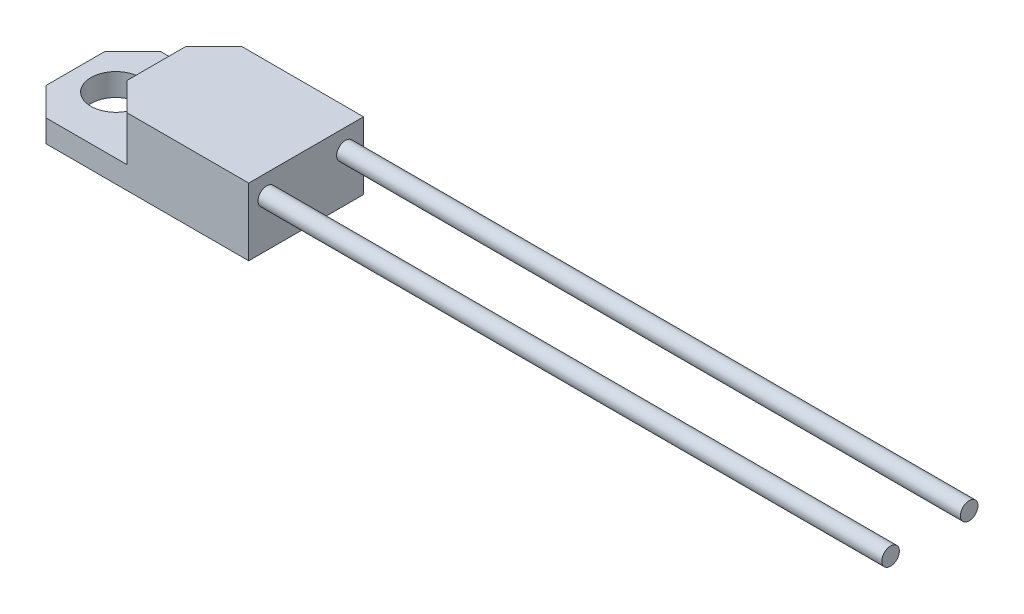
SolidWorks part; units mm, degrees
ref_plane "Front Plane" through (0, 0, 0) normal (0, 0, 1) x (1, 0, 0)
ref_plane "Top Plane" through (0, 0, 0) normal (0, 1, 0) x (1, 0, 0)
ref_plane "Right Plane" through (0, 0, 0) normal (1, 0, 0) x (0, 0, -1)
sketch "Sketch1" plane through (0, 0, 0) normal (0, 1, 0) x (1, 0, 0)
  line L1 (-9.25, -4.6) -> (9.25, -4.6)
  line L2 (-9.25, -4.6) -> (-9.25, 4.6)
  line L3 (-9.25, 4.6) -> (9.25, 4.6)
  line L4 (9.25, -4.6) -> (9.25, 4.6)
  line L5 (-9.25, -4.6) -> (9.25, 4.6) construction
  line L6 (-9.25, 4.6) -> (9.25, -4.6) construction
  point P0 (0, 0)
  dimension "D1" = 18.5
  dimension "D2" = 9.2
extrude "Boss-Extrude1" add sketch "Sketch1" along normal blind 1.8
sketch "Sketch3" plane through (0, 1.8, 0) normal (0, 1, 0) x (1, 0, 0)
  line L0 (-9.25, -4.6) -> (9.25, -4.6) construction
  line L1 (9.25, 4.6) -> (-2.75, 4.6)
  line L2 (9.25, 4.6) -> (9.25, -4.6)
  line L3 (9.25, -4.6) -> (-2.75, -4.6)
  line L4 (-2.75, 4.6) -> (-2.75, -4.6)
  dimension "D1" = 12
extrude "Boss-Extrude3" add sketch "Sketch3" along normal blind 3.6
sketch "Sketch2" plane through (9.25, 0, 0) normal (1, 0, 0) x (0, 0, -1)
  line L0 (-4.6, 3.78) -> (4.6, 3.78) construction
  line L3 (0, 1.8) -> (0, 0) construction
  line L4 (-4.6, 1.8) -> (4.6, 1.8) construction
  line L5 (-4.6, 0) -> (4.6, 0) construction
  circle A0 centre (-3.15, 3.78) radius 0.705
  circle A1 centre (3.15, 3.78) radius 0.705
  dimension "D1" = 1.41
  dimension "D2" = 1.41
  dimension "D3" = 3.15
  dimension "D4" = 3.15
  dimension "D5" = 3.78
extrude "Boss-Extrude2" add sketch "Sketch2" along normal blind 50
sketch "Sketch4" plane through (0, 1.8, 0) normal (0, 1, 0) x (1, 0, 0)
  line L0 (-9.25, 0) -> (-2.75, 0) construction
  line L1 (-9.25, 4.6) -> (-9.25, -4.6) construction
  line L2 (-2.75, 4.6) -> (-2.75, -4.6) construction
  circle A0 centre (-6, 0) radius 2
  dimension "D1" = 4
extrude "Cut-Extrude1" cut sketch "Sketch4" against normal through all
chamfer "Chamfer1" distance 2.25 angle 45 4 edges at (-9.25, 0.9, -4.6) (-9.25, 0.9, 4.6)
